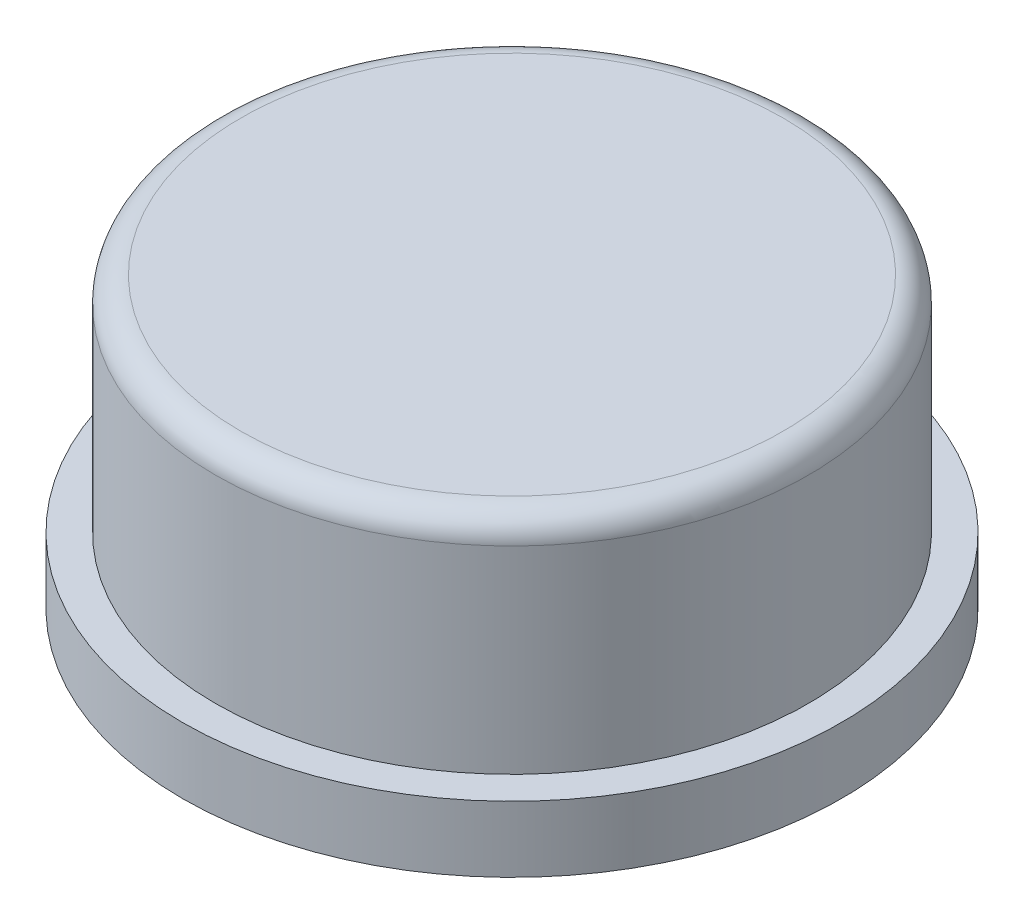
SolidWorks part; units mm, degrees
ref_plane "Спереди" through (0, 0, 0) normal (0, 0, 1) x (1, 0, 0)
ref_plane "Сверху" through (0, 0, 0) normal (0, 1, 0) x (1, 0, 0)
ref_plane "Справа" through (0, 0, 0) normal (1, 0, 0) x (0, 0, -1)
sketch "Эскиз5" plane through (0, 0, 0) normal (0, 1, 0) x (1, 0, 0)
  circle A0 centre (0, 0) radius 6.5
  dimension "D1" = 13
extrude "Бобышка-Вытянуть5" add sketch "Эскиз5" along normal blind 1.3
sketch "Эскиз6" plane through (0, 1.3, 0) normal (0, 1, 0) x (1, 0, 0)
  circle A0 centre (0, 0) radius 5.85
  dimension "D1" = 11.7
extrude "Бобышка-Вытянуть6" add sketch "Эскиз6" along normal blind 4.4
fillet "Скругление2" radius 0.5 1 edges at (0, 5.7, 5.85)
sketch "Эскиз7" plane through (0, 0, 0) normal (0, -1, 0) x (1, 0, 0)
  line L1 (-2, 2) -> (2, 2)
  line L2 (-2, 2) -> (-2, -2)
  line L3 (-2, -2) -> (2, -2)
  line L4 (2, 2) -> (2, -2)
  line L5 (-2, 2) -> (2, -2) construction
  line L6 (-2, -2) -> (2, 2) construction
  point P0 (0, 0)
  dimension "D1" = 4
  dimension "D2" = 4
extrude "Бобышка-Вытянуть7" add sketch "Эскиз7" along normal blind 2
sketch "Эскиз8" plane through (0, -2, 0) normal (0, -1, 0) x (1, 0, 0)
  line L1 (-1.9, 1.9) -> (1.9, 1.9)
  line L2 (-1.9, 1.9) -> (-1.9, -1.9)
  line L3 (-1.9, -1.9) -> (1.9, -1.9)
  line L4 (1.9, 1.9) -> (1.9, -1.9)
  line L5 (-1.9, 1.9) -> (1.9, -1.9) construction
  line L6 (-1.9, -1.9) -> (1.9, 1.9) construction
  point P0 (0, 0)
  dimension "D1" = 3.8
  dimension "D2" = 3.8
extrude "Вырез-Вытянуть1" cut sketch "Эскиз8" against normal blind 2
